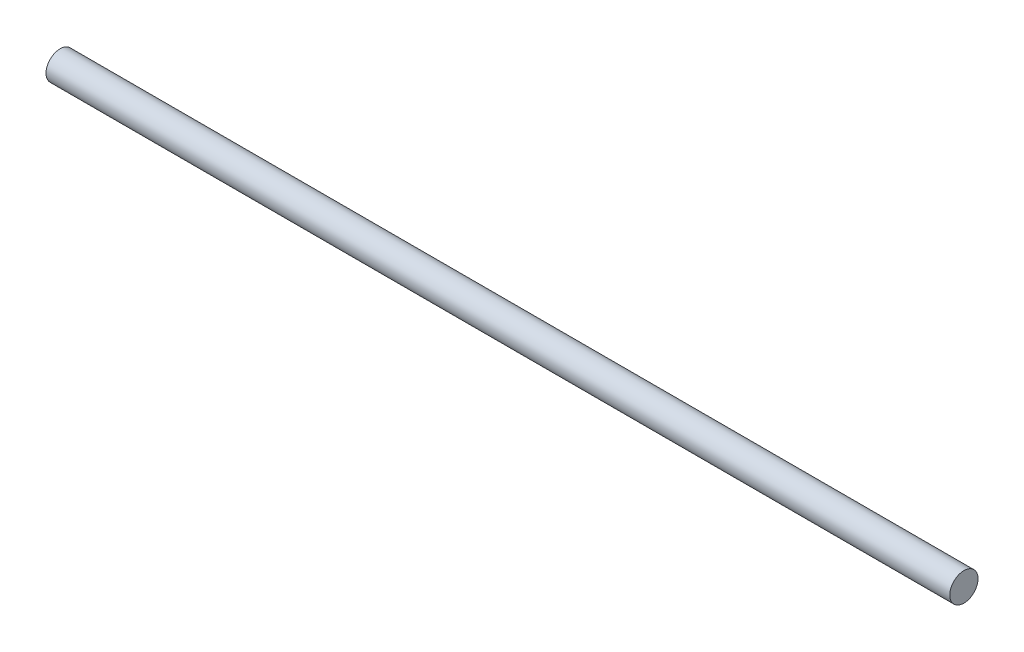
SolidWorks part; units mm, degrees
ref_plane "Front Plane" through (0, 0, 0) normal (0, 0, 1) x (1, 0, 0)
ref_plane "Top Plane" through (0, 0, 0) normal (0, 1, 0) x (1, 0, 0)
ref_plane "Right Plane" through (0, 0, 0) normal (1, 0, 0) x (0, 0, -1)
sketch "Sketch1" plane through (0, 0, 0) normal (0, 1, 0) x (1, 0, 0)
  line L0 (0, 0) -> (-609.6, 0)
  dimension "D1" = 609.6
sweep "Sweep1" add path "Sketch1" circular profile diameter 19.05 parameters "D3"=19.05
